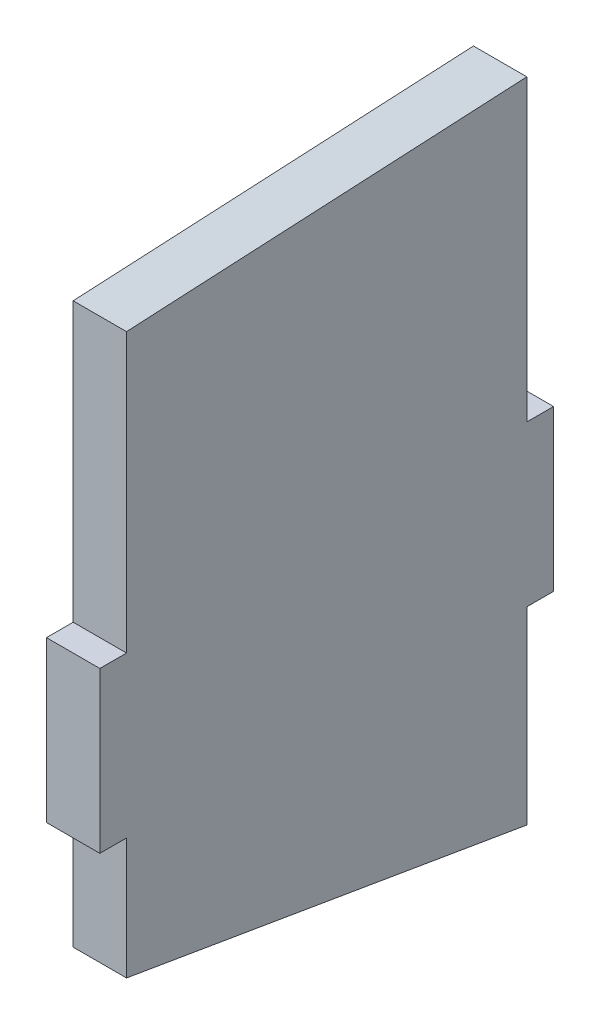
SolidWorks part; units mm, degrees
material "Pink Foam"
ref_plane "Front Plane" through (0, 0, 0) normal (0, 0, 1) x (1, 0, 0)
ref_plane "Top Plane" through (0, 0, 0) normal (0, 1, 0) x (1, 0, 0)
ref_plane "Right Plane" through (0, 0, 0) normal (1, 0, 0) x (0, 0, -1)
sketch "Sketch1" plane through (0, 0, 0) normal (1, 0, 0) x (0, 0, -1)
  line L0 (-95.25, 170.5633) -> (95.25, 180.3237)
  line L1 (-95.25, -203.2) -> (95.25, -203.2)
  line L2 (-95.25, -203.2) -> (-95.25, 203.2)
  line L3 (-95.25, 203.2) -> (95.25, 203.2)
  line L4 (95.25, -203.2) -> (95.25, 203.2)
  line L5 (-95.25, -203.2) -> (95.25, 203.2) construction
  line L6 (-95.25, 203.2) -> (95.25, -203.2) construction
  line L7 (-107.95, -38.1) -> (107.95, -38.1)
  line L8 (-107.95, -38.1) -> (-107.95, 38.1)
  line L9 (-107.95, 38.1) -> (107.95, 38.1)
  line L10 (107.95, -38.1) -> (107.95, 38.1)
  line L11 (-107.95, -38.1) -> (107.95, 38.1) construction
  line L12 (-107.95, 38.1) -> (107.95, -38.1) construction
  line L14 (-95.25, -95.8238) -> (95.25, -128.0296)
  point P0 (0, 0)
  point P6 (0, 0)
  dimension "D1" = 190.5
  dimension "D2" = 215.9
  dimension "D3" = 76.2
  dimension "D4" = 406.4
  dimension "D5" = 32.6367
  dimension "D6" = 22.8763
  dimension "D7" = 75.1704
  dimension "D8" = 266.3871
extrude "Boss-Extrude1" add sketch "Sketch1" along normal blind 25.4 contours L2 L9 L4 L0 | L7 L10 L9 L4 | L9 L2 L7 L4 | L9 L8 L7 L2 | L2 L14 L4 L7
